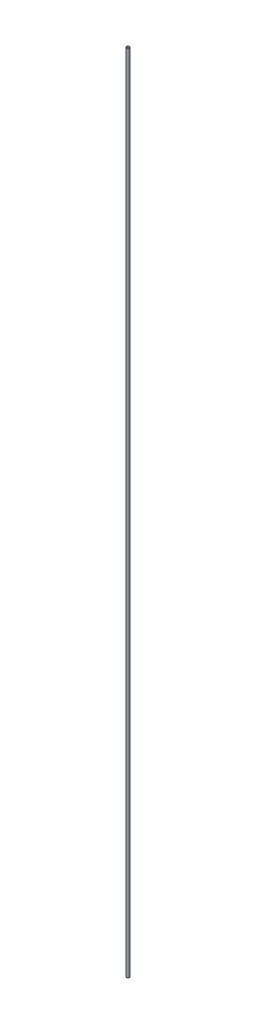
SolidWorks part; units mm, degrees
ref_plane "Front Plane" through (0, 0, 0) normal (0, 0, 1) x (1, 0, 0)
ref_plane "Top Plane" through (0, 0, 0) normal (0, 1, 0) x (1, 0, 0)
ref_plane "Right Plane" through (0, 0, 0) normal (1, 0, 0) x (0, 0, -1)
sketch "Sketch1" plane through (0, 0, 0) normal (0, 1, 0) x (1, 0, 0)
  circle A0 centre (0, 0) radius 3.175
  circle A1 centre (0, 0) radius 3.027
  dimension "D1" = 6.35
sketch "Sketch2" plane through (0, 0, 0) normal (1, 0, 0) x (0, 0, -1)
  line L0 (0, 0) -> (0, -1828.8)
  dimension "D1" = 1828.8
sweep "Sweep1" add profiles "Sketch1" path "Sketch2"
